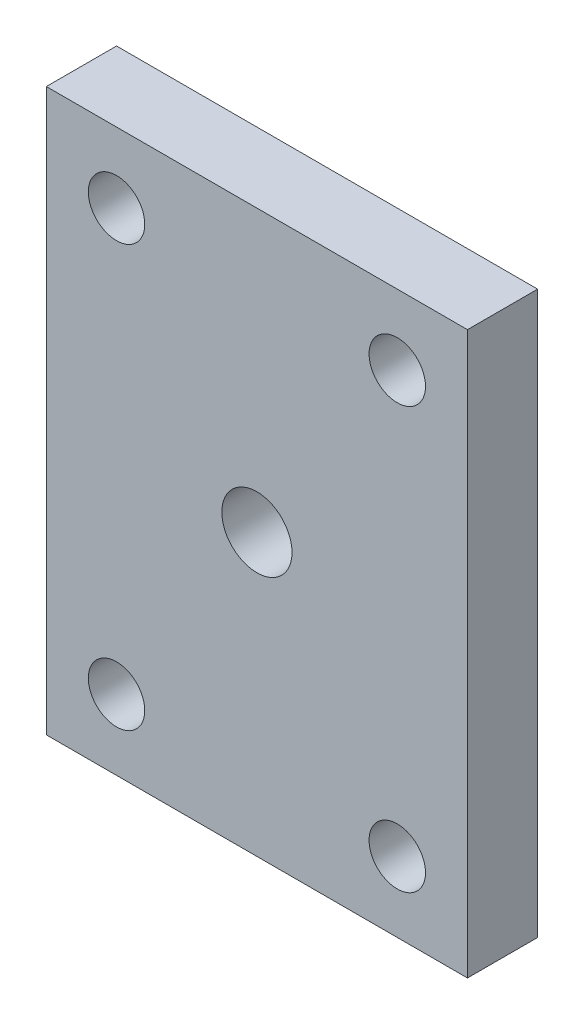
SolidWorks part; units mm, degrees
ref_plane "Front Plane" through (0, 0, 0) normal (0, 0, 1) x (1, 0, 0)
ref_plane "Top Plane" through (0, 0, 0) normal (0, 1, 0) x (1, 0, 0)
ref_plane "Right Plane" through (0, 0, 0) normal (1, 0, 0) x (0, 0, -1)
sketch "Sketch2" plane through (0, 0, 0) normal (0, 0, 1) x (1, 0, 0)
  line L0 (6.35, 44.45) -> (31.75, 44.45) construction
  line L1 (0, 0) -> (38.1, 0)
  line L2 (0, 0) -> (0, 50.8)
  line L3 (0, 50.8) -> (38.1, 50.8)
  line L4 (38.1, 0) -> (38.1, 50.8)
  line L5 (31.75, 44.45) -> (31.75, 6.35) construction
  line L6 (31.75, 6.35) -> (6.35, 6.35) construction
  line L7 (6.35, 6.35) -> (6.35, 44.45) construction
  circle A0 centre (19.05, 25.4) radius 3.175
  circle A1 centre (6.35, 44.45) radius 2.5527
  circle A2 centre (31.75, 44.45) radius 2.5527
  circle A3 centre (31.75, 6.35) radius 2.5527
  circle A4 centre (6.35, 6.35) radius 2.5527
  dimension "D3" = 6.35
  dimension "D4" = 5.1054
  dimension "D5" = 5.1054
  dimension "D6" = 5.1054
  dimension "D7" = 5.1054
  dimension "D1" = 50.8
  dimension "D2" = 38.1
  dimension "D8" = 19.05
  dimension "D9" = 25.4
  dimension "D10" = 25.4
  dimension "D11" = 38.1
  dimension "D12" = 6.35
  dimension "D13" = 6.35
extrude "Boss-Extrude1" add sketch "Sketch2" along normal blind 6.35
